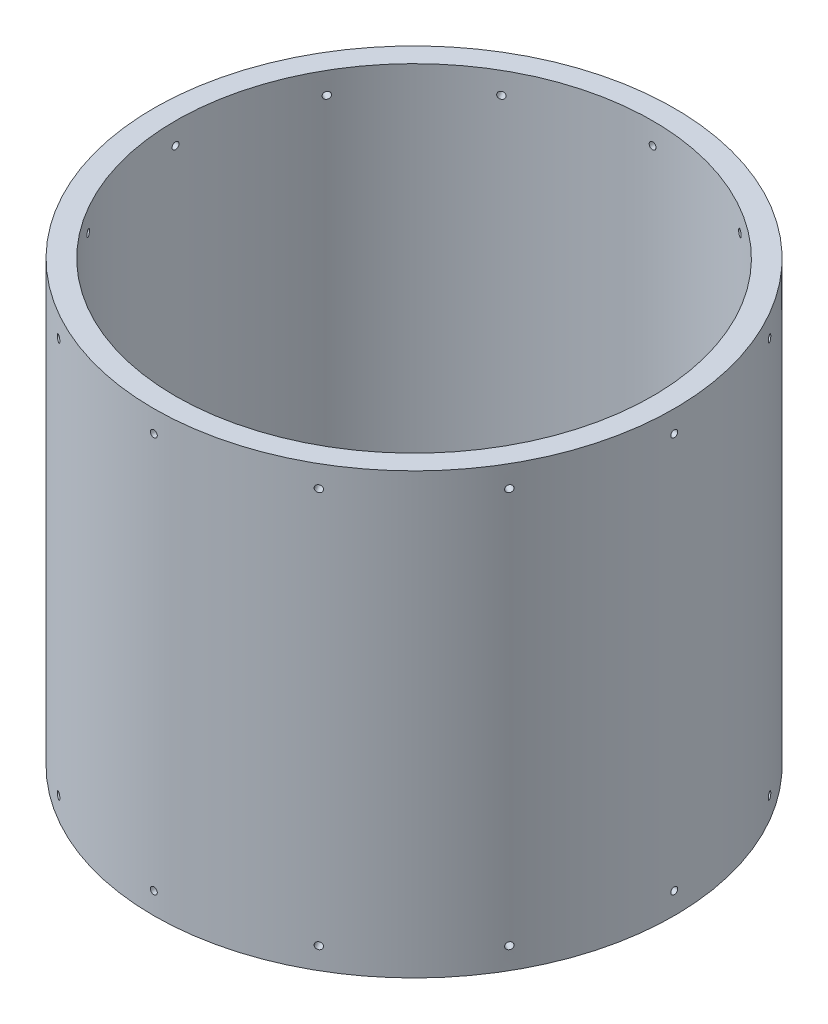
SolidWorks part; units mm, degrees
ref_plane "Front Plane" through (0, 0, 0) normal (0, 0, 1) x (1, 0, 0)
ref_plane "Top Plane" through (0, 0, 0) normal (0, 1, 0) x (1, 0, 0)
ref_plane "Right Plane" through (0, 0, 0) normal (1, 0, 0) x (0, 0, -1)
sketch "Sketch1" plane through (0, 0, 0) normal (0, 1, 0) x (1, 0, 0)
  circle A0 centre (0, 0) radius 152.4
  circle A1 centre (0, 0) radius 139.7
  dimension "D1" = 304.8
  dimension "D2" = 279.4
extrude "Boss-Extrude1" add sketch "Sketch1" along normal blind 257.175
ref_plane "Plane1" through (152.4, 0, 0) normal (1, 0, 0) x (0, 0, -1)
sketch "Sketch2" plane through (152.4, 0, 0) normal (1, 0, 0) x (0, 0, -1)
  line L0 (0, 323.4357) -> (0, -45.9614) construction
  line L1 (-152.4, 0) -> (152.4, 0) construction
  line L2 (152.4, 257.175) -> (-152.4, 257.175) construction
  line L3 (-152.4, 0) -> (152.4, 0) construction
  line L4 (152.4, 257.175) -> (-152.4, 257.175) construction
hole_wizard "#10-32 Tapped Hole1" positions "3DSketch1" profile "Sketch3" tap size "#10-32" standard "ANSI Inch"
sketch3d "3DSketch1"
  line L0 (152.4, 323.4357, 0) -> (152.4, -45.9614, 0) construction
  line L1 (152.4, 257.175, -152.4) -> (152.4, 257.175, 152.4) construction
  line L2 (152.4, 0, 152.4) -> (152.4, 0, -152.4) construction
  point P0 (152.4, 244.475, 0)
  point P2 (152.4, 12.7, 0)
  dimension "D1" = 12.7
  dimension "D2" = 12.7
sketch "Sketch3" plane through (152.4, 244.475, 0) normal (0, 1, 0) x (0, 0, -1)
  line L0 (0, 0) -> (0, 343.2351)
  line L1 (0, 343.2351) -> (2.0193, 343.2351)
  line L2 (2.0193, 343.2351) -> (2.0193, 0)
  line L5 (2.0193, 0) -> (0, 0)
  line L11 (0, -6.35) -> (0, 107.95) construction
  dimension "Thru Tap Drill Dia." = 4.0386
  dimension "Thru Tap Drill Depth" = 343.2351
cosmetic thread "Hole Thread1" parameters "D2"=4.826
cosmetic thread "Hole Thread2" parameters "D2"=4.826
pattern_circular "CirPattern1" count 12 over 360 about axis through (0, 257.175, 0) along (0, -1, 0) of "#10-32 Tapped Hole1"
